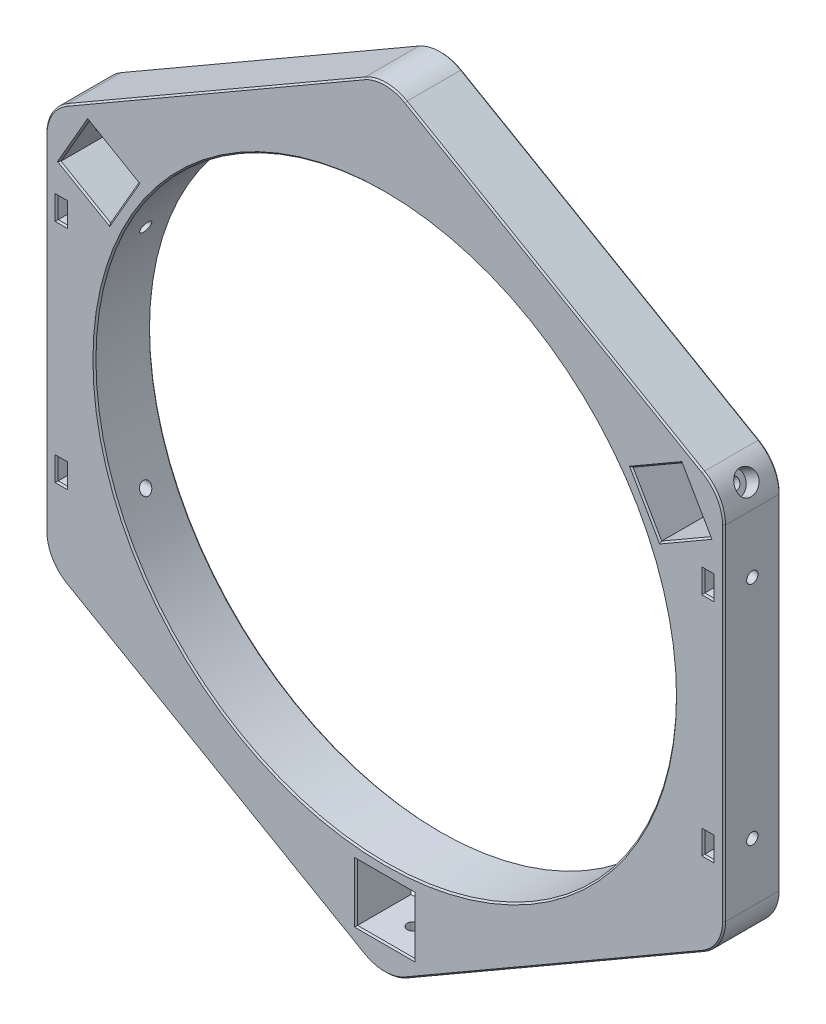
SolidWorks part; units mm, degrees
ref_plane "Top Plane" through (0, 0, 0) normal (0, 0, 1) x (1, 0, 0)
ref_plane "Front Plane" through (0, 0, 0) normal (0, 1, 0) x (1, 0, 0)
ref_plane "Right Plane" through (0, 0, 0) normal (1, 0, 0) x (0, 0, -1)
sketch "Sketch1" plane through (0, 0, 0) normal (0, 0, 1) x (1, 0, 0)
  line L0 (0, 0) -> (0, 121.7219) construction
  line L1 (0, 0) -> (107.9732, 62.3384) construction
  line L2 (0, 0) -> (110.8259, -63.9854) construction
  line L3 (0, 0) -> (0, -117.8434) construction
  line L4 (0, 0) -> (-109.5488, -63.248) construction
  line L5 (0, 0) -> (-114.2494, 65.9619) construction
  line L6 (0, 103.923) -> (90, 51.9615)
  line L7 (90, 51.9615) -> (90, -51.9615)
  line L8 (90, -51.9615) -> (0, -103.923)
  line L9 (0, -103.923) -> (-90, -51.9615)
  line L10 (-90, -51.9615) -> (-90, 51.9615)
  line L11 (-90, 51.9615) -> (0, 103.923)
  circle A0 centre (0, 0) radius 77
  circle A1 centre (0, 0) radius 103.923 construction
  dimension "D1" = 154
  dimension "D4" = 180
  dimension "D2" = 60
  dimension "D3" = 60
extrude "Boss-Extrude1" add sketch "Sketch1" along normal blind 15
sketch "Sketch2" plane through (0, 0, 15) normal (0, 0, 1) x (1, 0, 0)
  line L0 (0, 0) -> (0, -120.5827) construction
  line L1 (-7.6, -80) -> (7.6, -80)
  line L2 (-7.6, -80) -> (-7.6, -95.2)
  line L3 (-7.6, -95.2) -> (7.6, -95.2)
  line L4 (7.6, -80) -> (7.6, -95.2)
  line L5 (-7.6, -80) -> (7.6, -95.2) construction
  line L6 (-7.6, -95.2) -> (7.6, -80) construction
  line L7 (-65.482, 46.5818) -> (-73.082, 33.4182)
  line L8 (-65.482, 46.5818) -> (-78.6456, 54.1818)
  line L9 (-78.6456, 54.1818) -> (-86.2456, 41.0182)
  line L10 (-73.082, 33.4182) -> (-86.2456, 41.0182)
  line L11 (-65.482, 46.5818) -> (-86.2456, 41.0182) construction
  line L12 (-78.6456, 54.1818) -> (-73.082, 33.4182) construction
  line L13 (73.082, 33.4182) -> (65.482, 46.5818)
  line L14 (73.082, 33.4182) -> (86.2456, 41.0182)
  line L15 (86.2456, 41.0182) -> (78.6456, 54.1818)
  line L16 (65.482, 46.5818) -> (78.6456, 54.1818)
  line L17 (73.082, 33.4182) -> (78.6456, 54.1818) construction
  line L18 (86.2456, 41.0182) -> (65.482, 46.5818) construction
  point P0 (0, -87.6)
  point P8 (-75.8638, 43.8)
  point P15 (75.8638, 43.8)
  point P20 (0, 0)
  dimension "D1" = 80
  dimension "D2" = 15.2
  dimension "D3" = 15.2
  dimension "D4" = 3
extrude "Cut-Extrude1" cut sketch "Sketch2" against normal through all
fillet "Fillet1" radius 11.11 6 edges at (-90, -51.9615, 7.5) (-90, 51.9615, 7.5) (0, 103.923, 7.5) (90, 51.9615, 7.5) (90, -51.9615, 7.5) (0, -103.923, 7.5)
ref_plane "Plane1" through (0, 0, 0) normal (-0.866, 0.5, 0) x (0, 0, -1)
sketch "Sketch9" plane through (-82.4456, 47.6, 0) normal (0.866, -0.5, 0) x (0, 0, -1)
  line L0 (0, 0) -> (-36.7336, 0) construction
  line L2 (-15, 7.6) -> (-15, -7.6) construction
  circle A0 centre (-7.5, 0) radius 1.5
  dimension "D1" = 3
  dimension "D2" = 7.5
extrude "Cut-Extrude6" cut sketch "Sketch9" against normal blind 3
sketch "Sketch10" plane through (-85.0437, 49.1, 0) normal (0.866, -0.5, 0) x (0, 0, -1)
  circle A0 centre (-7.5, 0) radius 3
  dimension "D1" = 6
extrude "Cut-Extrude7" cut sketch "Sketch10" against normal through all
pattern_circular "CirPattern2" count 3 over 360 about axis through (0, 0, 0) along (0, 0, 1) of "Cut-Extrude6", "Cut-Extrude7"
sketch "Sketch13" plane through (-90, 0, 0) normal (-1, 0, 0) x (0, 0, 1)
  line L0 (7.5, 71.8396) -> (7.5, -65.74) construction
  line L1 (0, 0) -> (22.0952, 0) construction
  circle A0 centre (7.5, -30) radius 1.5
  circle A1 centre (7.5, 30) radius 1.5
  dimension "D3" = 3
  dimension "D1" = 7.5
  dimension "D2" = 30
  dimension "D4" = 30
extrude "Cut-Extrude10" cut sketch "Sketch13" against normal through all
sketch "Sketch14" plane through (0, 0, 15) normal (0, 0, 1) x (1, 0, 0)
  line L0 (-93.0465, 30) -> (-77.4171, 30) construction
  line L1 (-87, 32.8) -> (-84.5, 32.8)
  line L2 (-87, 32.8) -> (-87, 27.2)
  line L3 (-87, 27.2) -> (-84.5, 27.2)
  line L4 (-84.5, 32.8) -> (-84.5, 27.2)
  line L9 (-70.262, 31.5) -> (-90, 31.5) construction
  line L10 (-90, 28.5) -> (-71.5315, 28.5) construction
  line L11 (-90, 45.5472) -> (-90, -45.5472) construction
  line L12 (8.25, 0) -> (-8.25, 0) construction
  line L13 (-93.0465, -30) -> (-77.4171, -30) construction
  line L14 (-84.5, -32.8) -> (-84.5, -27.2)
  line L15 (-87, -27.2) -> (-84.5, -27.2)
  line L16 (-87, -32.8) -> (-87, -27.2)
  line L17 (-87, -32.8) -> (-84.5, -32.8)
  line L18 (0, -8.25) -> (0, 8.25) construction
  line L19 (93.0465, -30) -> (77.4171, -30) construction
  line L20 (93.0465, 30) -> (77.4171, 30) construction
  line L21 (87, -32.8) -> (84.5, -32.8)
  line L22 (87, -32.8) -> (87, -27.2)
  line L23 (87, -27.2) -> (84.5, -27.2)
  line L24 (84.5, -32.8) -> (84.5, -27.2)
  line L25 (84.5, 32.8) -> (84.5, 27.2)
  line L26 (87, 27.2) -> (84.5, 27.2)
  line L27 (87, 32.8) -> (87, 27.2)
  line L28 (87, 32.8) -> (84.5, 32.8)
  dimension "D1" = 2.5
  dimension "D2" = 5.6
  dimension "D3" = 3
extrude "Cut-Extrude11" cut sketch "Sketch14" against normal through all
chamfer "Chamfer1" distance 0.4 angle 45 82 edges at (0, -102.2043, 0) (45, -77.9423, 0) (88.5115, -51.1022, 0) (90, 0, 0) (88.5115, 51.1022, 0) (45, 77.9423, 0) (0, 102.2043, 0) (-45, 77.9423, 0) (-88.5115, 51.1022, 0) (-90, 0, 0) (-88.5115, -51.1022, 0) (-45, -77.9423, 0) (82.4456, 47.6, 0) (79.6638, 37.2182, 0) (69.282, 40, 0) (72.0638, 50.3818, 0) (-82.4456, 47.6, 0) (-72.0638, 50.3818, 0) (-69.282, 40, 0) (-79.6638, 37.2182, 0) (0, -95.2, 0) (-7.6, -87.6, 0) (0, -80, 0) (7.6, -87.6, 0) (77, 0, 0) (77, 0, 15) (-88.5115, 51.1022, 15) (-45, 77.9423, 15) (0, 102.2043, 15) (45, 77.9423, 15) (88.5115, 51.1022, 15) (90, 0, 15) (88.5115, -51.1022, 15) (45, -77.9423, 15) (0, -102.2043, 15) (-45, -77.9423, 15) (-88.5115, -51.1022, 15) (-90, 0, 15) (79.6638, 37.2182, 15) (82.4456, 47.6, 15) (72.0638, 50.3818, 15) (69.282, 40, 15) (-72.0638, 50.3818, 15) (-82.4456, 47.6, 15) (-79.6638, 37.2182, 15) (-69.282, 40, 15) (-7.6, -87.6, 15) (0, -95.2, 15) (7.6, -87.6, 15) (0, -80, 15) (-84.5, 30, 15) (-85.75, 32.8, 15) (-87, 30, 15) (-85.75, 27.2, 15) (-85.75, -27.2, 15) (-87, -30, 15) (-85.75, -32.8, 15) (-84.5, -30, 15) (84.5, -30, 15) (85.75, -32.8, 15) (87, -30, 15) (85.75, -27.2, 15) (85.75, 27.2, 15) (87, 30, 15) (85.75, 32.8, 15) (84.5, 30, 15) (-85.75, 32.8, 0) (-84.5, 30, 0) (-85.75, 27.2, 0) (-87, 30, 0) (-87, -30, 0) (-85.75, -27.2, 0) (-84.5, -30, 0) (-85.75, -32.8, 0) (85.75, -32.8, 0) (84.5, -30, 0) (85.75, -27.2, 0) (87, -30, 0) (87, 30, 0) (85.75, 27.2, 0) (84.5, 30, 0) (85.75, 32.8, 0)
equation "\"H\"=15"
equation "\"D1@Boss-Extrude1\"=\"H\""
equation "\"D2@Sketch9\"=\"H\"/2"
